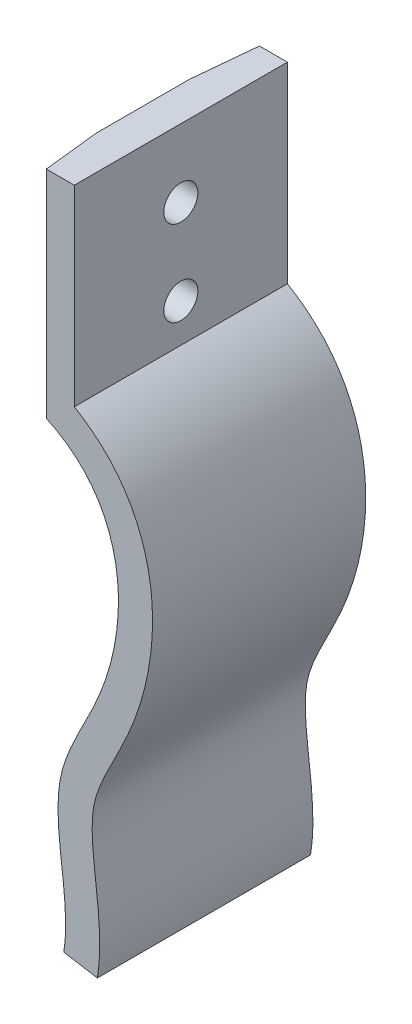
SolidWorks part; units mm, degrees
ref_plane "Ön Düzlem" through (0, 0, 0) normal (0, 0, 1) x (1, 0, 0)
ref_plane "Üst Düzlem" through (0, 0, 0) normal (0, 1, 0) x (1, 0, 0)
ref_plane "Sağ Düzlem" through (0, 0, 0) normal (1, 0, 0) x (0, 0, -1)
sketch "Çizim1" plane through (0, 0, 0) normal (0, 0, 1) x (1, 0, 0)
  line L0 (0, 46.8099) -> (0, 21.8099)
  line L1 (4, 46.8099) -> (4, 24.2964)
  line L2 (0, 46.8099) -> (4, 46.8099)
  line L3 (2.7684, -31.7069) -> (6.7145, -32.3612)
  spline S0 degree 3 poles (0, 21.8099) (10.5687, 17.4853) (10.8615, 0.8206) (0.9983, -13.7254) (2.7959, -23.6402) (3.1211, -29.5799) (2.7684, -31.7069) knots 0 0 0 0 0.502232 0.695448 0.885833 1 1 1 1
  spline S1 degree 1 poles (4, 24.2964) (6.7145, -32.3612) knots 0 0 1 1 construction
  spline S2 degree 3 poles (4, 24.2964) (4.6852, 23.9004) (6.022, 23.0113) (8.3339, 20.9926) (10.609, 18.0309) (12.3264, 14.0662) (13.1595, 9.9108) (13.2499, 5.7018) (12.7186, 1.5308) (11.8331, -1.8486) (10.899, -4.4521) (9.8104, -6.9845) (8.3727, -9.7588) (7.2043, -12.1465) (6.5751, -13.8552) (6.2779, -15.001) (6.1214, -16.211) (6.0652, -18.048) (6.2666, -20.675) (6.7224, -24.2353) (7.0119, -27.48) (6.9828, -30.2151) (6.8312, -31.6574) (6.7145, -32.3612) knots 0.033865 0.033865 0.033865 0.033865 0.064056 0.094248 0.154631 0.215015 0.275398 0.335782 0.396165 0.456549 0.486741 0.516932 0.577316 0.637699 0.667891 0.698083 0.728274 0.758466 0.81885 0.879233 0.939617 0.969808 1 1 1 1
  dimension "D2" = 25
  dimension "D1" = 4
extrude "Yükseklik-Ekstrüzyon1" add sketch "Çizim1" along normal blind 25
sketch "Çizim2" plane through (4, 0, 0) normal (1, 0, 0) x (0, 0, -1)
  line L0 (-25, 24.2964) -> (-25, 46.8099) construction
  line L1 (-25, 46.8099) -> (0, 46.8099) construction
  circle A0 centre (-12.5, 38.8099) radius 2
  circle A1 centre (-12.5, 28.8099) radius 2
  dimension "D1" = 12.5
  dimension "D3" = 10
  dimension "D4" = 4
  dimension "D2" = 8
extrude "Kes-Ekstrüzyon1" cut sketch "Çizim2" against normal blind 25
sketch "Çizim3" plane through (0, 46.8099, 0) normal (0, 1, 0) x (1, 0, 0)
  line L0 (0, 0) -> (0, -7.4868)
  line L1 (0, -25) -> (0, 0) construction
  line L2 (0, -7.4868) -> (0.7211, 0)
  line L3 (4, 0) -> (0, 0) construction
  line L4 (0.7211, 0) -> (0, 0)
  line L5 (0, -25) -> (0, -18.4293)
  line L6 (0, -18.4293) -> (0.7211, -25)
  line L7 (4, -25) -> (0, -25) construction
  line L8 (0.7211, -25) -> (0, -25)
extrude "Kes-Ekstrüzyon2" cut sketch "Çizim3" against normal blind 40
